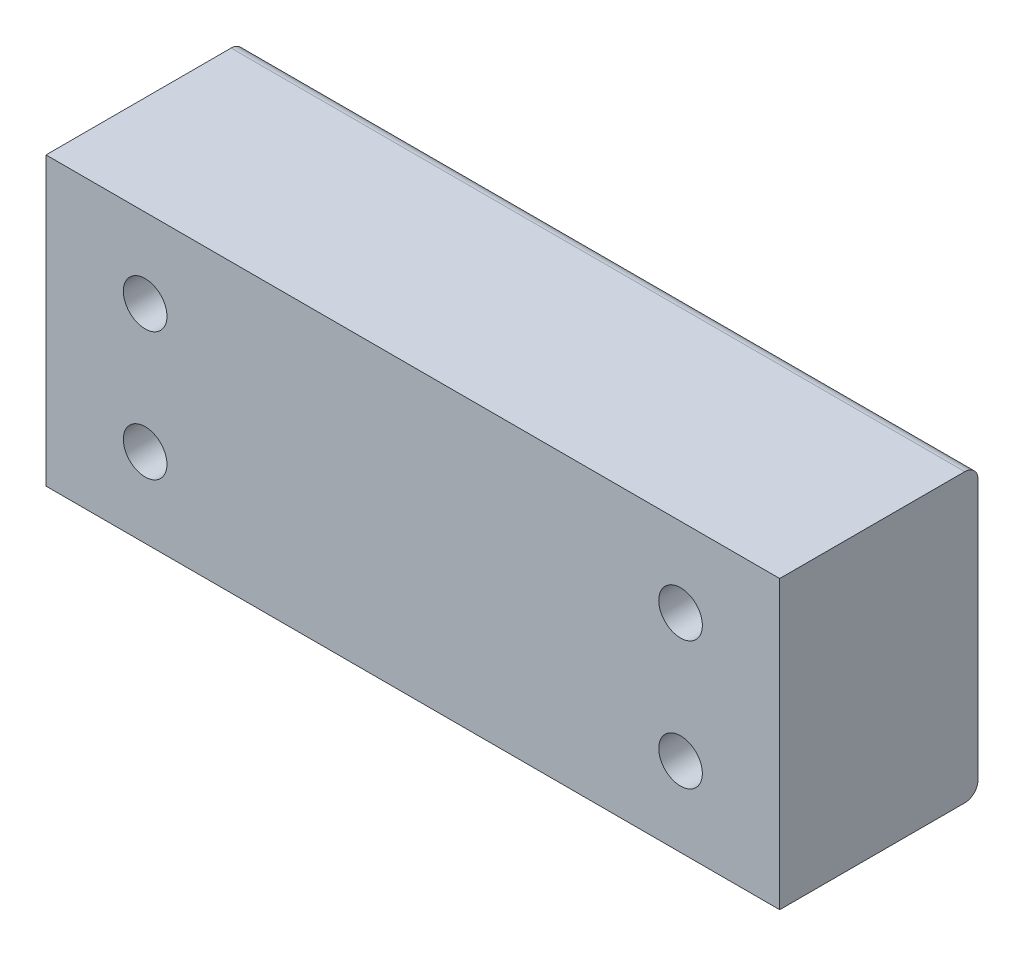
SolidWorks part; units mm, degrees
material "PETG"
ref_plane "Front Plane" through (0, 0, 0) normal (0, 0, 1) x (1, 0, 0)
ref_plane "Top Plane" through (0, 0, 0) normal (0, 1, 0) x (1, 0, 0)
ref_plane "Right Plane" through (0, 0, 0) normal (1, 0, 0) x (0, 0, -1)
sketch "Sketch1" plane through (0, 0, 0) normal (0, 0, 1) x (1, 0, 0)
  line L1 (-27.75, -10.85) -> (27.75, -10.85)
  line L2 (-27.75, -10.85) -> (-27.75, 10.85)
  line L3 (-27.75, 10.85) -> (27.75, 10.85)
  line L4 (27.75, -10.85) -> (27.75, 10.85)
  line L5 (-27.75, -10.85) -> (27.75, 10.85) construction
  line L6 (-27.75, 10.85) -> (27.75, -10.85) construction
  point P0 (0, 0)
  dimension "D1" = 55.5
  dimension "D2" = 21.7
extrude "Boss-Extrude1" add sketch "Sketch1" along normal blind 15
sketch "Sketch3" plane through (0, 0, 15) normal (0, 0, 1) x (1, 0, 0)
  line L0 (-27.75, -10.85) -> (27.75, -10.85) construction
  line L1 (-27.75, 10.85) -> (-12.75, 10.85) construction
  line L2 (-27.75, 10.85) -> (-27.75, -10.85) construction
  line L3 (-27.75, -10.85) -> (-12.75, -10.85) construction
  line L4 (-12.75, 10.85) -> (-12.75, -10.85) construction
  line L5 (-20.25, -10.85) -> (-20.25, 10.85) construction
  line L6 (-27.75, 0) -> (-12.75, 0) construction
  line L7 (0, 10.85) -> (0, -10.85) construction
  line L8 (27.75, 10.85) -> (-27.75, 10.85) construction
  circle A0 centre (-20.25, 4.85) radius 1.65
  circle A8 centre (-20.25, -4.85) radius 1.65
  circle A9 centre (20.25, -4.85) radius 1.65
  circle A10 centre (20.25, 4.85) radius 1.65
  dimension "D2" = 3.3
  dimension "D3" = 6
  dimension "D1" = 15
extrude "Cut-Extrude1" cut sketch "Sketch3" against normal through all
fillet "Fillet1" radius 1 2 edges at (0, -10.85, 0) (0, 10.85, 0)
